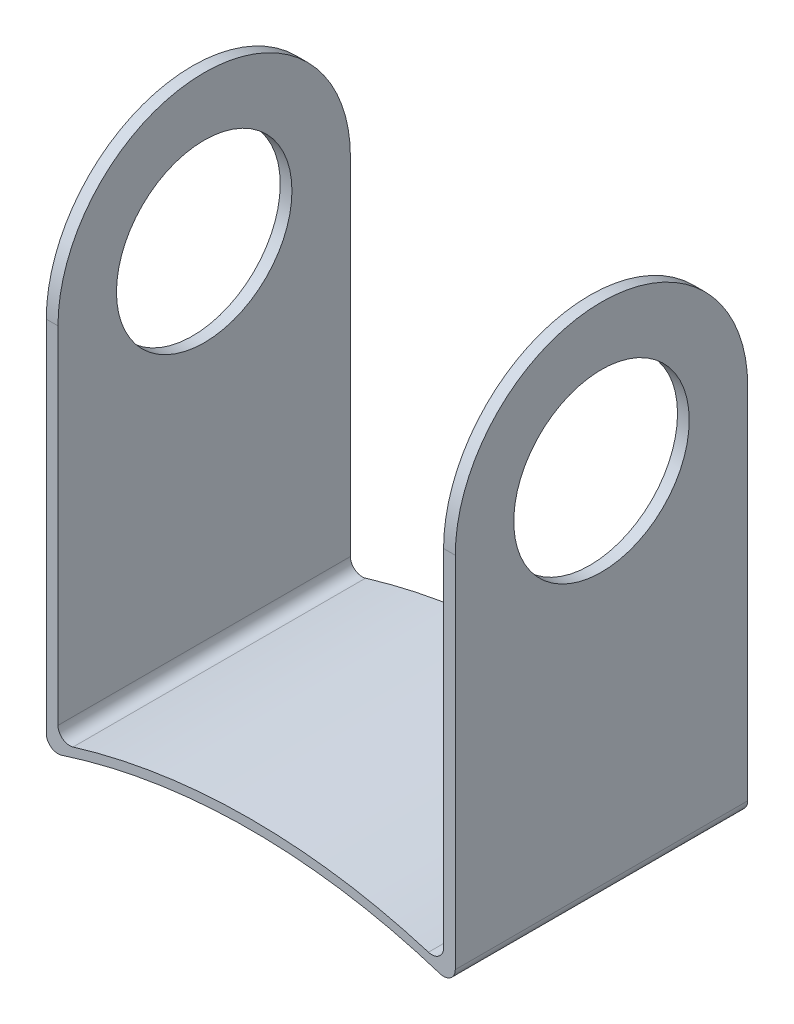
SolidWorks part; units mm, degrees
material "AISI 1020 Steel, Cold Rolled"
ref_plane "Front Plane" through (0, 0, 0) normal (0, 0, 1) x (1, 0, 0)
ref_plane "Top Plane" through (0, 0, 0) normal (0, 1, 0) x (1, 0, 0)
ref_plane "Right Plane" through (0, 0, 0) normal (1, 0, 0) x (0, 0, -1)
sketch "Sketch2" plane through (0, 0, 0) normal (0, 0, 1) x (1, 0, 0)
  line L0 (-5.691, 5.5764) -> (-5.691, 50)
  line L1 (27.2711, 5.5764) -> (27.2711, 49.569)
  line L2 (-6.691, 50) -> (-6.691, 4.4445)
  line L3 (-6.691, 50) -> (-5.691, 50)
  line L4 (28.2711, 4.4445) -> (28.2711, 49.569)
  line L5 (28.2711, 49.569) -> (27.2711, 49.569)
  arc A0 (-5.691, 5.5764) -> (27.2711, 5.5764) centre (10.7901, -43.9031) cw
  arc A1 (-6.691, 4.4445) -> (28.2711, 4.4445) centre (10.7901, -44.9031) cw
  point P4 (0, 0)
  dimension "D2" = 1
  dimension "D3" = 1
  dimension "D1" = 1
extrude "Boss-Extrude1" add sketch "Sketch2" along normal blind 25 contours L0 L3 L2 A1 L4 L5 L1 A0
fillet "Fillet1" radius 1 2 edges at (-6.691, 4.4445, 12.5) (28.2711, 4.4445, 12.5)
fillet "Fillet2" radius 1 2 edges at (27.2711, 5.5764, 12.5) (-5.691, 5.5764, 12.5)
fillet "Fillet3" radius 0.05 4 edges at (-6.691, 50, 12.5) (-5.691, 50, 12.5) (27.2711, 49.569, 12.5) (28.2711, 49.569, 12.5)
sketch "Sketch4" plane through (28.2711, 0, 0) normal (1, 0, 0) x (0, 0, -1)
  line L0 (-25, 36.519) -> (-25, 49.519)
  line L1 (-25, 5.8399) -> (-25, 49.519) construction
  line L3 (-25, 49.519) -> (0, 49.519)
  line L4 (0, 5.8399) -> (0, 49.519) construction
  line L5 (0, 49.519) -> (-25, 49.519) construction
  line L6 (0, 49.519) -> (0, 36.519)
  arc A0 (-25, 36.519) -> (0, 36.519) centre (-12.5, 36.519) cw
extrude "Cut-Extrude1" cut sketch "Sketch4" against normal through all
sketch "Sketch5" plane through (28.2711, 0, 0) normal (1, 0, 0) x (0, 0, -1)
  circle A0 centre (-12.5, 36.519) radius 7.5
extrude "Cut-Extrude2" cut sketch "Sketch5" against normal through all
